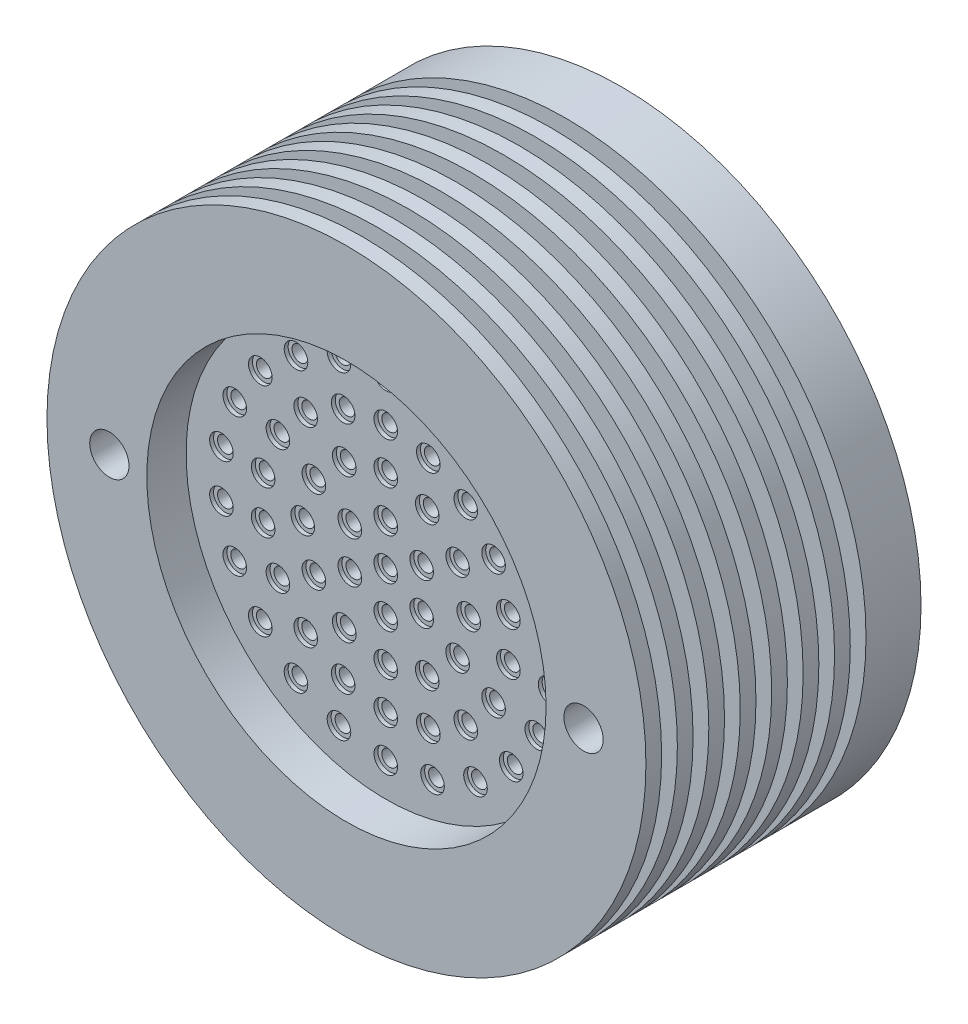
SolidWorks part; units mm, degrees
material "Alliage 1060"
ref_plane "Plan de face" through (0, 0, 0) normal (0, 0, 1) x (1, 0, 0)
ref_plane "Plan de dessus" through (0, 0, 0) normal (0, 1, 0) x (1, 0, 0)
ref_plane "Plan de droite" through (0, 0, 0) normal (1, 0, 0) x (0, 0, -1)
sketch "Esquisse2" plane through (0, 0, 0) normal (0, 0, 1) x (1, 0, 0)
  circle A0 centre (31.7399, 14.6188) radius 38.1
  dimension "D1" = 76.2
extrude "Boss.-Extru.1" add sketch "Esquisse2" along normal blind 35
sketch "Esquisse3" plane through (0, 0, 35) normal (0, 0, 1) x (1, 0, 0)
  line L0 (31.7399, 52.7188) -> (31.7399, -23.4812) construction
  circle A0 centre (31.7399, 14.6188) radius 38.1 construction
  circle A1 centre (31.7399, 14.6188) radius 25.4
  dimension "D1" = 50.8
extrude "Enlèv. mat.-Extru.1" cut sketch "Esquisse3" against normal blind 5
sketch "Esquisse4" plane through (0, 0, 0) normal (0, 0, -1) x (-1, 0, 0)
  line L0 (-31.7399, 52.7188) -> (-31.7399, -23.4812) construction
  circle A0 centre (-31.7399, 14.6188) radius 38.1 construction
  circle A1 centre (-31.7399, 14.6188) radius 25.4
  dimension "D1" = 50.8
extrude "Enlèv. mat.-Extru.2" cut sketch "Esquisse4" against normal offset from surface (25 mm away) 5 up to face at (57.1399, 14.6188, 30)
sketch "Esquisse5" plane through (0, 0, 30) normal (0, 0, 1) x (1, 0, 0)
  line L0 (31.7399, 40.0188) -> (31.7399, -10.7812) construction
  line L1 (31.7399, 14.6188) -> (31.7399, 19.8988) construction
  circle A0 centre (31.7399, 14.6188) radius 25.4 construction
  circle A1 centre (31.7399, 14.6188) radius 25.4 construction
  circle A2 centre (31.7399, 14.6188) radius 1
  circle A3 centre (31.7399, 19.8988) radius 1
  circle A4 centre (36.3125, 17.2588) radius 1
  circle A5 centre (36.3125, 11.9788) radius 1
  circle A6 centre (31.7399, 9.3388) radius 1
  circle A7 centre (27.1673, 11.9788) radius 1
  circle A8 centre (27.1673, 17.2588) radius 1
  circle A9 centre (31.7399, 25.1788) radius 1
  circle A10 centre (37.0199, 23.764) radius 1
  circle A11 centre (40.8851, 19.8988) radius 1
  circle A12 centre (42.2999, 14.6188) radius 1
  circle A13 centre (40.8851, 9.3388) radius 1
  circle A14 centre (37.0199, 5.4736) radius 1
  circle A15 centre (31.7399, 4.0588) radius 1
  circle A16 centre (26.4599, 5.4736) radius 1
  circle A17 centre (22.5946, 9.3388) radius 1
  circle A18 centre (21.1799, 14.6188) radius 1
  circle A19 centre (22.5946, 19.8988) radius 1
  circle A20 centre (26.4599, 23.764) radius 1
  circle A21 centre (31.7399, 30.4588) radius 1
  circle A22 centre (37.1575, 29.5035) radius 1
  circle A23 centre (41.9216, 26.7529) radius 1
  circle A24 centre (45.4577, 22.5388) radius 1
  circle A25 centre (47.3392, 17.3694) radius 1
  circle A26 centre (47.3392, 11.8682) radius 1
  circle A27 centre (45.4577, 6.6988) radius 1
  circle A28 centre (41.9216, 2.4846) radius 1
  circle A29 centre (37.1575, -0.2659) radius 1
  circle A30 centre (31.7399, -1.2212) radius 1
  circle A31 centre (26.3223, -0.2659) radius 1
  circle A32 centre (21.5581, 2.4846) radius 1
  circle A33 centre (18.022, 6.6988) radius 1
  circle A34 centre (16.1405, 11.8682) radius 1
  circle A35 centre (16.1405, 17.3694) radius 1
  circle A36 centre (18.022, 22.5388) radius 1
  circle A37 centre (21.5581, 26.7529) radius 1
  circle A38 centre (26.3223, 29.5035) radius 1
  circle A39 centre (31.7399, 35.7388) radius 1
  circle A40 centre (37.6901, 34.8833) radius 1
  circle A41 centre (43.1582, 32.3861) radius 1
  circle A42 centre (47.7013, 28.4494) radius 1
  circle A43 centre (50.9513, 23.3923) radius 1
  circle A44 centre (52.6449, 17.6245) radius 1
  circle A45 centre (52.6449, 11.6131) radius 1
  circle A46 centre (50.9513, 5.8452) radius 1
  circle A47 centre (47.7013, 0.7881) radius 1
  circle A48 centre (43.1582, -3.1485) radius 1
  circle A49 centre (37.6901, -5.6457) radius 1
  circle A50 centre (31.7399, -6.5012) radius 1
  circle A51 centre (25.7897, -5.6457) radius 1
  circle A52 centre (20.3215, -3.1485) radius 1
  circle A53 centre (15.7784, 0.7881) radius 1
  circle A54 centre (12.5284, 5.8452) radius 1
  circle A55 centre (10.8348, 11.6131) radius 1
  circle A56 centre (10.8348, 17.6245) radius 1
  circle A57 centre (12.5284, 23.3923) radius 1
  circle A58 centre (15.7784, 28.4494) radius 1
  circle A59 centre (20.3215, 32.3861) radius 1
  circle A60 centre (25.7897, 34.8833) radius 1
  point P24 (31.7399, 14.6188)
  point P49 (31.7399, 14.6188)
  point P86 (31.7399, 14.6188)
  point P131 (31.7399, 14.6188)
  dimension "D1" = 2
  dimension "D3" = 2
  dimension "D7" = 2
  dimension "D8" = 2
  dimension "D11" = 2
  dimension "D2" = 5.28
  dimension "D5" = 10.56
  dimension "D9" = 15.84
  dimension "D12" = 21.12
  dimension "D4" = 6
  dimension "D6" = 12
  dimension "D10" = 18
  dimension "D13" = 22
extrude "Enlèv. mat.-Extru.3" cut sketch "Esquisse5" against normal up to surface (5 mm away) up to face at (57.1399, 14.6188, 25)
sketch "Esquisse6" plane through (0, 0, 30) normal (0, 0, 1) x (1, 0, 0)
  circle A0 centre (31.7399, 14.6188) radius 1.5
  circle A1 centre (31.7399, 19.8988) radius 1.5
  circle A2 centre (36.3125, 17.2588) radius 1.5
  circle A3 centre (36.3125, 11.9788) radius 1.5
  circle A4 centre (31.7399, 9.3388) radius 1.5
  circle A5 centre (27.1673, 11.9788) radius 1.5
  circle A6 centre (27.1673, 17.2588) radius 1.5
  circle A7 centre (31.7399, 25.1788) radius 1.5
  circle A8 centre (37.0199, 23.764) radius 1.5
  circle A9 centre (40.8851, 19.8988) radius 1.5
  circle A10 centre (42.2999, 14.6188) radius 1.5
  circle A11 centre (40.8851, 9.3388) radius 1.5
  circle A12 centre (37.0199, 5.4736) radius 1.5
  circle A13 centre (31.7399, 4.0588) radius 1.5
  circle A14 centre (26.4599, 5.4736) radius 1.5
  circle A15 centre (22.5946, 9.3388) radius 1.5
  circle A16 centre (21.1799, 14.6188) radius 1.5
  circle A17 centre (22.5946, 19.8988) radius 1.5
  circle A18 centre (26.4599, 23.764) radius 1.5
  circle A19 centre (31.7399, 30.4588) radius 1.5
  circle A20 centre (31.7399, 35.7388) radius 1.5
  circle A21 centre (37.6901, 34.8833) radius 1.5
  circle A22 centre (43.1582, 32.3861) radius 1.5
  circle A23 centre (47.7013, 28.4494) radius 1.5
  circle A24 centre (50.9513, 23.3923) radius 1.5
  circle A25 centre (52.6449, 17.6245) radius 1.5
  circle A26 centre (52.6449, 11.6131) radius 1.5
  circle A27 centre (50.9513, 5.8452) radius 1.5
  circle A28 centre (47.7013, 0.7881) radius 1.5
  circle A29 centre (43.1582, -3.1485) radius 1.5
  circle A30 centre (37.6901, -5.6457) radius 1.5
  circle A31 centre (31.7399, -6.5012) radius 1.5
  circle A32 centre (25.7897, -5.6457) radius 1.5
  circle A33 centre (20.3215, -3.1485) radius 1.5
  circle A34 centre (15.7784, 0.7881) radius 1.5
  circle A35 centre (12.5284, 5.8452) radius 1.5
  circle A36 centre (10.8348, 11.6131) radius 1.5
  circle A37 centre (10.8348, 17.6245) radius 1.5
  circle A38 centre (12.5284, 23.3923) radius 1.5
  circle A39 centre (15.7784, 28.4494) radius 1.5
  circle A40 centre (20.3215, 32.3861) radius 1.5
  circle A41 centre (25.7897, 34.8833) radius 1.5
  circle A42 centre (37.1575, 29.5035) radius 1.5
  circle A43 centre (41.9216, 26.7529) radius 1.5
  circle A44 centre (45.4577, 22.5388) radius 1.5
  circle A45 centre (47.3392, 17.3694) radius 1.5
  circle A46 centre (47.3392, 11.8682) radius 1.5
  circle A47 centre (45.4577, 6.6988) radius 1.5
  circle A48 centre (41.9216, 2.4846) radius 1.5
  circle A49 centre (37.1575, -0.2659) radius 1.5
  circle A50 centre (31.7399, -1.2212) radius 1.5
  circle A51 centre (26.3223, -0.2659) radius 1.5
  circle A52 centre (21.5581, 2.4846) radius 1.5
  circle A53 centre (18.022, 6.6988) radius 1.5
  circle A54 centre (16.1405, 11.8682) radius 1.5
  circle A55 centre (16.1405, 17.3694) radius 1.5
  circle A56 centre (18.022, 22.5388) radius 1.5
  circle A57 centre (21.5581, 26.7529) radius 1.5
  circle A58 centre (26.3223, 29.5035) radius 1.5
  point P19 (31.7399, 14.6188)
  point P44 (31.7399, 14.6188)
  point P94 (31.7399, 14.6188)
  point P128 (31.7399, 14.6188)
  dimension "D1" = 3
  dimension "D2" = 3
  dimension "D4" = 3
  dimension "D6" = 3
  dimension "D7" = 3
  dimension "D3" = 6
  dimension "D5" = 12
  dimension "D8" = 22
  dimension "D9" = 18
extrude "Enlèv. mat.-Extru.4" cut sketch "Esquisse6" against normal blind 0.5
ref_plane "Plan1" through (0, 0, 33) normal (0, 0, 1) x (1, 0, 0)
sketch "Esquisse7" plane through (0, 0, 33) normal (0, 0, 1) x (1, 0, 0)
  circle A0 centre (31.7399, 14.6188) radius 38.1
  circle A1 centre (31.7399, 14.6188) radius 34.925
  dimension "D1" = 76.2
  dimension "D2" = 3.175
extrude "Enlèv. mat.-Extru.5" cut sketch "Esquisse7" against normal blind 2
pattern_linear "Répétition linéaire1" count 7 spacing 4 along (0, 0, -1) of "Enlèv. mat.-Extru.5"
sketch "Esquisse8" plane through (0, 0, 0) normal (0, 0, -1) x (-1, 0, 0)
  line L0 (-69.8399, 14.6188) -> (6.3601, 14.6188) construction
  circle A0 centre (-31.7399, 14.6188) radius 38.1 construction
  circle A1 centre (-1.5774, 14.6188) radius 2.5
  circle A2 centre (-61.9024, 14.6188) radius 2.5
  point P7 (-31.7399, 14.6188)
  point P13 (-31.7399, 14.6188)
  dimension "D3" = 5
  dimension "D1" = 30.1625
  dimension "D2" = 2
extrude "Enlèv. mat.-Extru.6" cut sketch "Esquisse8" against normal through all
